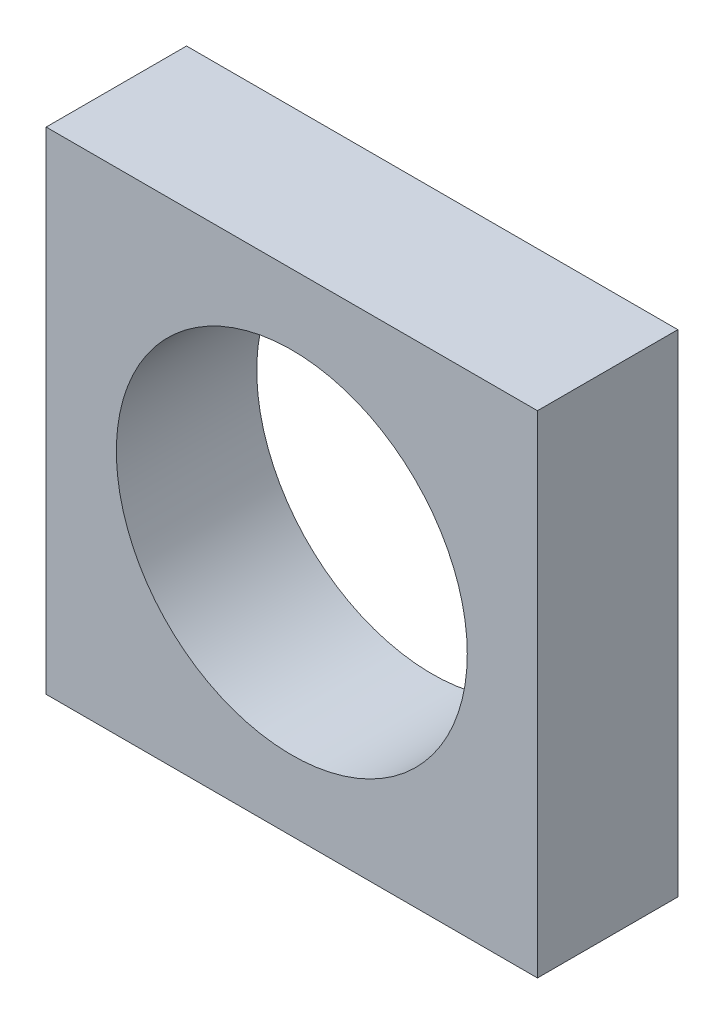
SolidWorks part; units mm, degrees
ref_plane "Front Plane" through (0, 0, 0) normal (0, 0, 1) x (1, 0, 0)
ref_plane "Top Plane" through (0, 0, 0) normal (0, 1, 0) x (1, 0, 0)
ref_plane "Right Plane" through (0, 0, 0) normal (1, 0, 0) x (0, 0, -1)
sketch "Sketch1" plane through (0, 0, 0) normal (0, 0, 1) x (1, 0, 0)
  line L1 (-3.5, 3.5) -> (3.5, 3.5)
  line L2 (-3.5, 3.5) -> (-3.5, -3.5)
  line L3 (-3.5, -3.5) -> (3.5, -3.5)
  line L4 (3.5, 3.5) -> (3.5, -3.5)
  line L5 (-3.5, 3.5) -> (3.5, -3.5) construction
  line L6 (-3.5, -3.5) -> (3.5, 3.5) construction
  circle A0 centre (0, 0) radius 2.5
  point P0 (0, 0)
  dimension "D2" = 5
  dimension "D1" = 7
extrude "Boss-Extrude1" add sketch "Sketch1" along normal mid plane 2
